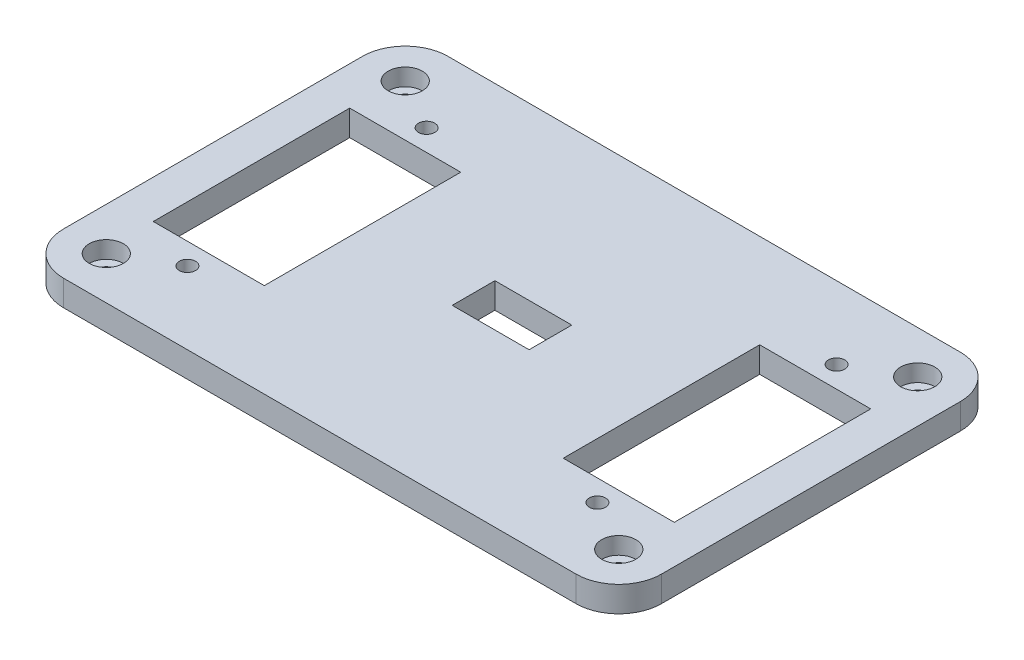
SolidWorks part; units mm, degrees
ref_plane "前视基准面" through (0, 0, 0) normal (0, 0, 1) x (1, 0, 0)
ref_plane "上视基准面" through (0, 0, 0) normal (0, 1, 0) x (1, 0, 0)
ref_plane "右视基准面" through (0, 0, 0) normal (1, 0, 0) x (0, 0, -1)
sketch "草图1" plane through (0, 0, 0) normal (0, 1, 0) x (1, 0, 0)
  line L1 (-35, 22.5) -> (35, 22.5)
  line L2 (-35, 22.5) -> (-35, -22.5)
  line L3 (-35, -22.5) -> (35, -22.5)
  line L4 (35, 22.5) -> (35, -22.5)
  line L5 (-35, 22.5) -> (35, -22.5) construction
  line L6 (-35, -22.5) -> (35, 22.5) construction
  point P0 (0, 0)
  dimension "D1" = 70
  dimension "D2" = 45
extrude "凸台-拉伸1" add sketch "草图1" along normal blind 3
ref_plane "基准面1" through (0, 3, 0) normal (0, 1, 0) x (1, 0, 0)
sketch "草图2" plane through (0, 3, 0) normal (0, 1, 0) x (1, 0, 0)
  line L0 (35, 22.5) -> (-35, 22.5) construction
  line L1 (17.5, 11.5) -> (30.5, 11.5)
  line L2 (17.5, 11.5) -> (17.5, -11.5)
  line L3 (17.5, -11.5) -> (30.5, -11.5)
  line L4 (30.5, 11.5) -> (30.5, -11.5)
  line L5 (35, -22.5) -> (35, 22.5) construction
  line L6 (-30.5, 11.5) -> (-17.5, 11.5)
  line L7 (-30.5, 11.5) -> (-30.5, -11.5)
  line L8 (-30.5, -11.5) -> (-17.5, -11.5)
  line L9 (-17.5, 11.5) -> (-17.5, -11.5)
  dimension "D1" = 23
  dimension "D2" = 13
  dimension "D3" = 11
  dimension "D4" = 11
  dimension "D5" = 23
  dimension "D6" = 13
  dimension "D7" = 35
  dimension "D8" = 4.5
extrude "切除-拉伸1" cut sketch "草图2" against normal blind 10
sketch "草图3" plane through (0, 3, 0) normal (0, 1, 0) x (1, 0, 0)
  line L0 (-24, 11.5) -> (-24, 14) construction
  line L1 (-17.5, 11.5) -> (-30.5, 11.5) construction
  line L2 (-24, -11.5) -> (-24, -14) construction
  line L3 (-30.5, -11.5) -> (-17.5, -11.5) construction
  line L4 (24, 11.5) -> (24, 14) construction
  line L5 (30.5, 11.5) -> (17.5, 11.5) construction
  line L6 (24, -11.5) -> (24, -14) construction
  line L7 (17.5, -11.5) -> (30.5, -11.5) construction
  circle A0 centre (-24, 14) radius 0.95
  circle A1 centre (-24, -14) radius 0.95
  circle A2 centre (24, 14) radius 0.95
  circle A3 centre (24, -14) radius 0.95
  dimension "D2" = 1.9
  dimension "D4" = 1.9
  dimension "D7" = 1.9
  dimension "D8" = 1.9
  dimension "D1" = 2.5
  dimension "D3" = 2.5
  dimension "D5" = 2.5
  dimension "D6" = 2.5
extrude "切除-拉伸2" cut sketch "草图3" against normal blind 10
fillet "圆角1" radius 5 1 edges at (35, 1.5, -22.5)
fillet "圆角2" radius 5 3 edges at (-35, 1.5, -22.5) (-35, 1.5, 22.5) (35, 1.5, 22.5)
sketch "草图4" plane through (0, 3, 0) normal (0, 1, 0) x (1, 0, 0)
  circle A0 centre (-30, 17.5) radius 0.95
  circle A1 centre (30, 17.5) radius 0.95
  circle A2 centre (-30, -17.5) radius 0.95
  circle A3 centre (30, -17.5) radius 0.95
  dimension "D1" = 1.9
  dimension "D2" = 1.9
  dimension "D3" = 1.9
  dimension "D4" = 1.9
extrude "切除-拉伸3" cut sketch "草图4" against normal blind 10
sketch "草图5" plane through (0, 3, 0) normal (0, 1, 0) x (1, 0, 0)
  circle A0 centre (-30, 17.5) radius 2
  circle A1 centre (30, 17.5) radius 2
  circle A2 centre (-30, -17.5) radius 2
  circle A3 centre (30, -17.5) radius 2
  dimension "D1" = 4
  dimension "D2" = 4
  dimension "D3" = 4
  dimension "D4" = 4
extrude "切除-拉伸4" cut sketch "草图5" against normal blind 2
sketch "草图6" plane through (0, 3, 0) normal (0, 1, 0) x (1, 0, 0)
  line L1 (-4.5, 2.5) -> (4.5, 2.5)
  line L2 (-4.5, 2.5) -> (-4.5, -2.5)
  line L3 (-4.5, -2.5) -> (4.5, -2.5)
  line L4 (4.5, 2.5) -> (4.5, -2.5)
  line L5 (-4.5, 2.5) -> (4.5, -2.5) construction
  line L6 (-4.5, -2.5) -> (4.5, 2.5) construction
  point P0 (0, 0)
  dimension "D1" = 9
  dimension "D2" = 5
extrude "切除-拉伸5" cut sketch "草图6" against normal blind 14
